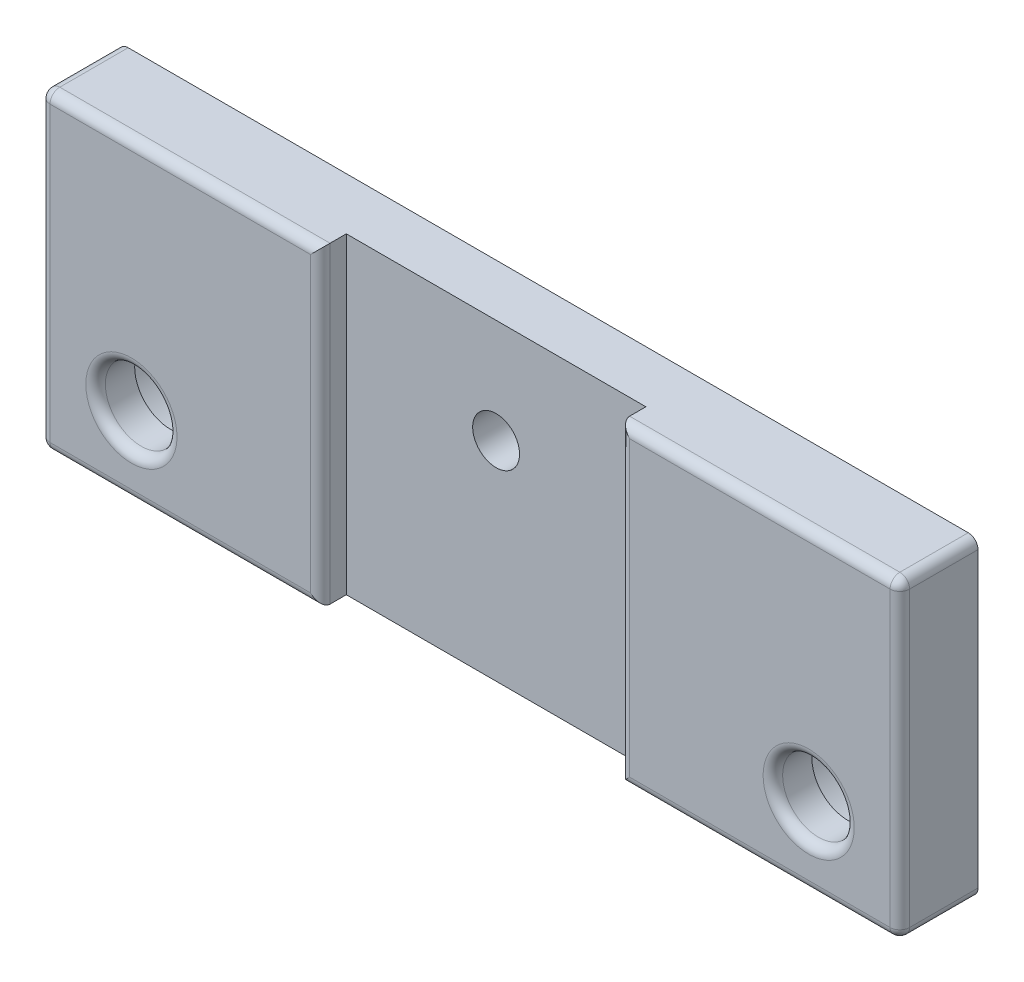
SolidWorks part; units mm, degrees
ref_plane "Plan de face" through (0, 0, 0) normal (0, 0, 1) x (1, 0, 0)
ref_plane "Plan de dessus" through (0, 0, 0) normal (0, 1, 0) x (1, 0, 0)
ref_plane "Plan de droite" through (0, 0, 0) normal (1, 0, 0) x (0, 0, -1)
sketch "Esquisse2" plane through (0, 0, 0) normal (0, 0, 1) x (1, 0, 0)
  line L1 (0, 0) -> (66, 0)
  line L2 (0, 0) -> (0, 24)
  line L3 (0, 24) -> (66, 24)
  line L4 (66, 0) -> (66, 24)
extrude "Boss.-Extru.1" add sketch "Esquisse2" along normal blind 6
sketch "Esquisse3" plane through (0, 0, 6) normal (0, 0, 1) x (1, 0, 0)
  line L1 (21.5, 0) -> (44.5, 0)
  line L2 (21.5, 0) -> (21.5, 24)
  line L3 (21.5, 24) -> (44.5, 24)
  line L4 (44.5, 0) -> (44.5, 24)
extrude "Enlèv. mat.-Extru.1" cut sketch "Esquisse3" against normal blind 2
sketch "Esquisse4" plane through (0, 0, 4) normal (0, 0, 1) x (1, 0, 0)
  circle A0 centre (33, 16) radius 1.8
extrude "Enlèv. mat.-Extru.2" cut sketch "Esquisse4" against normal through all
sketch "Esquisse5" plane through (0, 0, 0) normal (0, 0, -1) x (-1, 0, 0)
  circle A0 centre (-59, 6) radius 2.75
  circle A1 centre (-7, 6) radius 2.75
  point P4 (0, 0)
extrude "Enlèv. mat.-Extru.3" cut sketch "Esquisse5" against normal through all
sketch "Esquisse6" plane through (0, 0, 0) normal (0, 0, -1) x (-1, 0, 0)
  circle A0 centre (-59, 6) radius 5.1
  circle A1 centre (-7, 6) radius 5.1
extrude "Enlèv. mat.-Extru.4" cut sketch "Esquisse6" against normal blind 3
fillet "Congé1" radius 0.75 14 edges at (66, 12, 6) (55.25, 0, 6) (44.5, 12, 6) (55.25, 24, 6) (56.25, 6, 6) (0, 12, 6) (10.75, 24, 6) (21.5, 12, 6) (10.75, 0, 6) (4.25, 6, 6) (0, 24, 3) (0, 0, 3) (66, 0, 3) (66, 24, 3)
